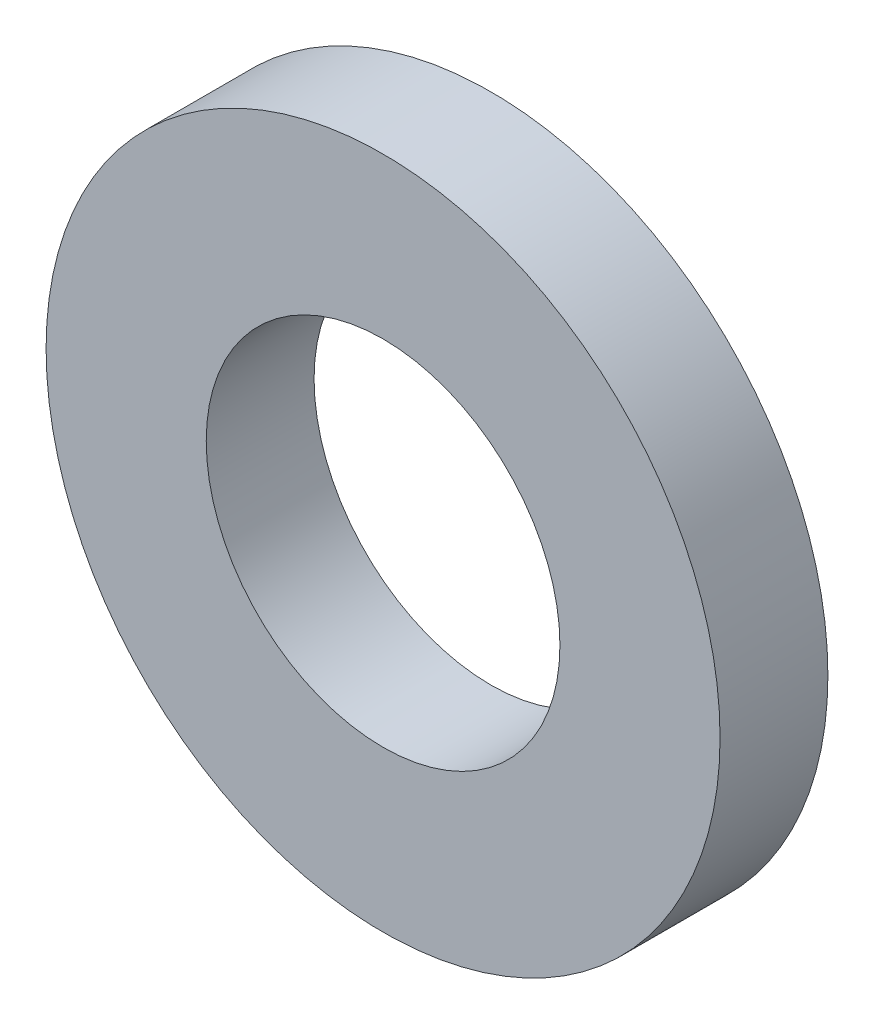
SolidWorks part; units mm, degrees
ref_plane "Front Plane" through (0, 0, 0) normal (0, 0, 1) x (1, 0, 0)
ref_plane "Top Plane" through (0, 0, 0) normal (0, 1, 0) x (1, 0, 0)
ref_plane "Right Plane" through (0, 0, 0) normal (1, 0, 0) x (0, 0, -1)
sketch "Sketch1" plane through (0, 0, 0) normal (0, 0, 1) x (1, 0, 0)
  circle A0 centre (0, 0) radius 2.0828
  circle A1 centre (0, 0) radius 3.9688
  dimension "ID" = 4.1656
  dimension "OD" = 7.9375
extrude "Extrude1" add sketch "Sketch1" against normal blind 1.27
